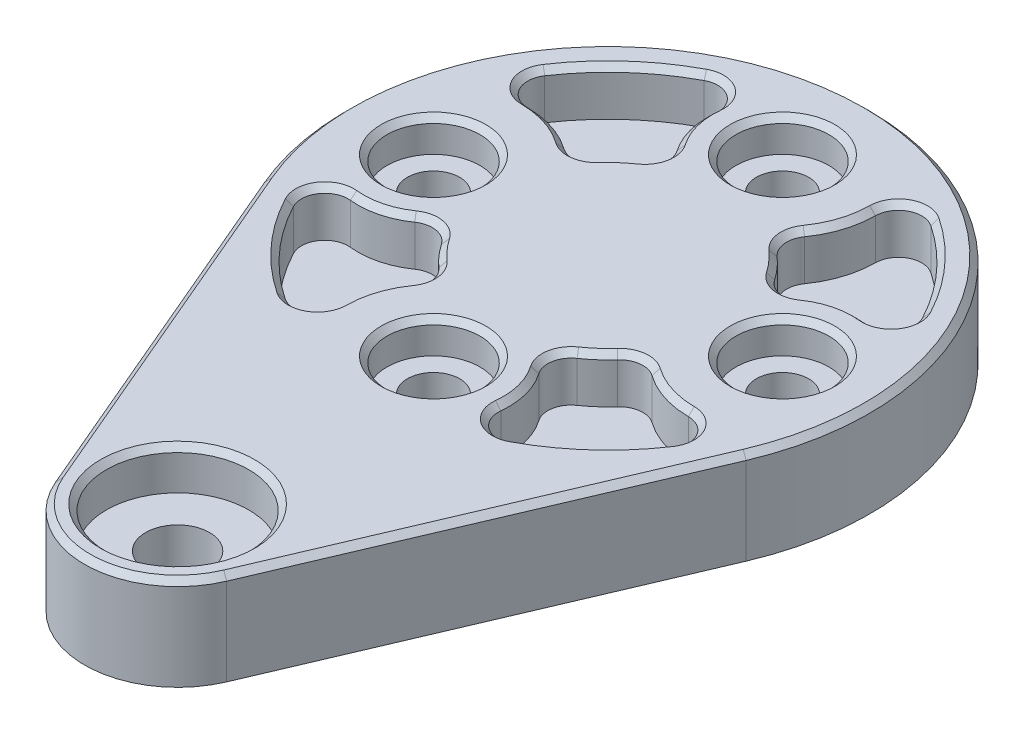
SolidWorks part; units mm, degrees
ref_plane "Front Plane" through (0, 0, 0) normal (0, 0, 1) x (1, 0, 0)
ref_plane "Top Plane" through (0, 0, 0) normal (0, 1, 0) x (1, 0, 0)
ref_plane "Right Plane" through (0, 0, 0) normal (1, 0, 0) x (0, 0, -1)
sketch "Sketch1" plane through (0, 0, 0) normal (0, 1, 0) x (0, 0, -1)
  line L0 (-3.1351, 7.3601) -> (28.1824, 20.7003)
  line L1 (-3.1351, -7.3601) -> (28.1824, -20.7003)
  circle A0 centre (0, 0) radius 8
  circle A1 centre (37, 0) radius 22.5
  point P9 (0, 8.2756)
  point P10 (0, 0)
  point P11 (0, 10.0626)
  point P12 (0, 0)
  point P13 (0, 8.2045)
  point P14 (-2.936, 6.9014)
  point P15 (-3.0405, 6.856)
  point P16 (-2.4524, -7.0877)
  dimension "D1" = 45
  dimension "D3" = 16
  dimension "D2" = 37
extrude "Boss-Extrude1" add sketch "Sketch1" along normal blind 8 contours A1 L0 A0 L1 | A0 | A1
sketch "Sketch2" plane through (0, 8, 0) normal (0, 1, 0) x (0, 0, -1)
  line L0 (22, 0) -> (52, 0) construction
  line L1 (37, 15) -> (37, -15) construction
  circle A0 centre (37, 0) radius 15
  arc A1 (28.1824, -20.7003) -> (28.1824, 20.7003) centre (37, 0) ccw construction
  point P9 (0, 0)
  dimension "D1" = 30
hole_wizard "CBORE for M4 Hex Head Cap Screw1" positions "Sketch5" profile "Sketch4" counterbore size "M4" standard "ISO" end condition through all
sketch "Sketch5" plane through (0, 8, 0) normal (0, 1, 0) x (0, 0, -1)
  point P0 (37, 15)
  point P3 (52, 0)
  point P6 (37, -15)
  point P9 (22, 0)
sketch "Sketch4" plane through (-15, 8, -37) normal (1, 0, 0) x (0, 0, 1)
  line L0 (0, 0) -> (0, 8)
  line L1 (0, 8) -> (2.25, 8)
  line L3 (2.25, 8) -> (2.25, 2.8)
  line L4 (2.25, 2.8) -> (4, 2.8)
  line L5 (4, 2.8) -> (4, 0)
  line L7 (4, 0) -> (0, 0)
  line L11 (0, -6.35) -> (0, 107.95) construction
  dimension "Thru Hole Dia." = 4.5
  dimension "Thru Hole Depth" = 8
  dimension "C'Bore Dia." = 8
  dimension "C'Bore Depth" = 2.8
hole_wizard "CBORE for M5 Hex Head Cap Screw1" positions "Sketch7" profile "Sketch8" counterbore size "M5" standard "ISO" end condition through all
sketch "Sketch7" plane through (0, 8, 0) normal (0, 1, 0) x (0, 0, -1)
  point P0 (0, 0)
sketch "Sketch8" plane through (0, 8, 0) normal (1, 0, 0) x (0, 0, 1)
  line L0 (0, 0) -> (0, 8)
  line L1 (0, 8) -> (2.75, 8)
  line L3 (2.75, 8) -> (2.75, 3.5)
  line L4 (2.75, 3.5) -> (6.119, 3.5)
  line L5 (6.119, 3.5) -> (6.119, 0)
  line L7 (6.119, 0) -> (0, 0)
  line L11 (0, -6.35) -> (0, 107.95) construction
  dimension "Thru Hole Dia." = 5.5
  dimension "Thru Hole Depth" = 8
  dimension "C'Bore Dia." = 12.238
  dimension "C'Bore Depth" = 3.5
sketch "Sketch9" plane through (0, 8, 0) normal (0, 1, 0) x (0, 0, -1)
  line L0 (22, 0) -> (52, 0) construction
  circle A12 centre (37, 15) radius 6.5
  arc A13 (32.2388, 19.425) -> (33.342, 9.627) centre (37, 15) ccw
  arc A22 (28.1202, 5.2163) -> (18.3222, 7.1512) centre (22, 0) ccw
  arc A26 (33.342, 9.627) -> (28.1202, 5.2163) centre (37, 0) ccw
  arc A28 (32.2388, 19.425) -> (18.3222, 7.1512) centre (37, 0) ccw
  dimension "D3" = 2.5
extrude "Cut-Extrude1" cut sketch "Sketch9" against normal blind 4
fillet "Fillet1" radius 2 4 edges at (-5.2163, 6, -28.1202) (-9.627, 6, -33.342) (-19.425, 6, -32.2388) (-7.1512, 6, -18.3222)
pattern_circular "CirPattern1" count 4 every 90 about axis through (0, 0, -37) along (0, 1, 0) of "Cut-Extrude1", "Fillet1"
chamfer "Chamfer1" distance 0.5 angle 45 41 edges at (8.9566, 8, -30.804) (12.5307, 8, -29.347) (16.7069, 8, -27.8937) (13.3959, 8, -22.149) (7.3345, 8, -19.4504) (6.2943, 8, -23.6223) (5.0011, 8, -27.2233) (6.8109, 8, -29.2752) (14.851, 8, -50.3959) (9.1063, 8, -53.7069) (7.653, 8, -49.5307) (6.196, 8, -45.9566) (17.5496, 8, -44.3345) (13.3777, 8, -43.2943) (9.7767, 8, -42.0011) (7.7248, 8, -43.8109) (-5.0011, 8, -46.7767) (-6.2943, 8, -50.3777) (-7.3345, 8, -54.5496) (-13.3959, 8, -51.851) (-16.7069, 8, -46.1063) (-12.5307, 8, -44.653) (-8.9566, 8, -43.196) (-6.8109, 8, -44.7248) (15, 8, -33) (0, 8, -48) (-15, 8, -33) (-17.5496, 8, -29.6655) (-13.3777, 8, -30.7057) (-9.7767, 8, -31.9989) (-7.7248, 8, -30.1891) (-6.196, 8, -28.0434) (-7.653, 8, -24.4693) (-9.1063, 8, -20.2931) (-14.851, 8, -23.6041) (0, 8, -18) (0, 8, 6.119) (0, 8, -59.5) (14.0302, 8, -12.5236) (0, 8, 8) (-14.0302, 8, -12.5236)
